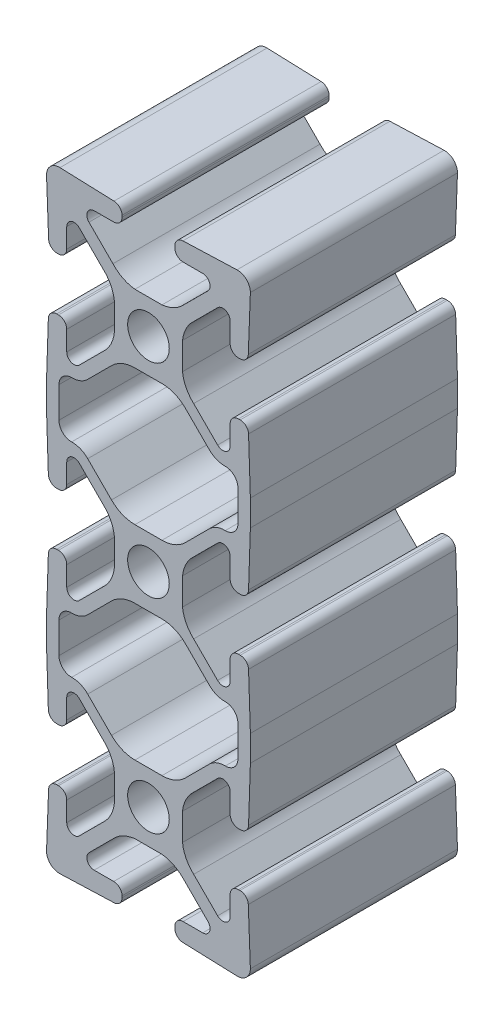
SolidWorks part; units mm, degrees
material "6061 Alloy"
ref_plane "Front" through (0, 0, 0) normal (0, 0, 1) x (1, 0, 0)
ref_plane "Top" through (0, 0, 0) normal (0, 1, 0) x (1, 0, 0)
ref_plane "Right" through (0, 0, 0) normal (1, 0, 0) x (0, 0, -1)
sketch "Sketch1" plane through (0, 0, 0) normal (0, 0, 1) x (1, 0, 0)
  line L0 (-7.4494, 41.7144) -> (-4.5322, 44.6317)
  line L1 (-1.6585, 45.822) -> (1.6585, 45.822)
  line L2 (-10.976, 35.6094) -> (-10.976, 39.3906)
  line L3 (4.5322, 44.6317) -> (7.4494, 41.7144)
  line L4 (-4.5322, 30.3683) -> (-7.4494, 33.2856)
  line L5 (10.976, 39.3906) -> (10.976, 35.6094)
  line L6 (1.6585, 29.178) -> (-1.6585, 29.178)
  line L7 (7.4494, 33.2856) -> (4.5322, 30.3683)
  line L8 (-12.5, 35.9125) -> (-12.5, 39.0875)
  line L9 (-12.2773, 29.22) -> (-12.5, 35.9125)
  line L10 (-12.5, 39.0875) -> (-12.2773, 45.78)
  line L11 (-11.036, 28.2385) -> (-11.2584, 28.2377)
  line L12 (-11.2584, 46.7622) -> (-11.036, 46.7615)
  line L13 (-10.02, 31.6575) -> (-10.02, 29.2545)
  line L14 (-10.02, 45.7455) -> (-10.02, 43.3425)
  line L15 (-5.5451, 29.3554) -> (-8.4836, 32.2939)
  line L16 (-8.4836, 42.7061) -> (-5.5451, 45.6446)
  line L17 (-4.178, 23.3415) -> (-4.178, 26.6585)
  line L18 (-4.178, 48.3415) -> (-4.178, 51.6585)
  line L19 (-8.4836, 17.7061) -> (-5.5451, 20.6446)
  line L20 (-5.5451, 54.3554) -> (-8.4836, 57.2939)
  line L21 (-10.02, 20.7455) -> (-10.02, 18.3425)
  line L22 (-10.02, 56.6575) -> (-10.02, 54.2545)
  line L23 (-11.2584, 21.7623) -> (-11.036, 21.7615)
  line L24 (-11.036, 53.2385) -> (-11.2263, 53.2379)
  line L25 (-12.5, 14.0875) -> (-12.2773, 20.78)
  line L26 (-12.2451, 54.2152) -> (-12.5, 60.9135)
  line L27 (-12.5, 10.9125) -> (-12.5, 14.0875)
  line L28 (-12.2773, 4.22) -> (-12.5, 10.9125)
  line L29 (-10.8555, 62.5) -> (-4.2218, 62.2615)
  line L30 (-11.036, 3.2385) -> (-11.2584, 3.2377)
  line L31 (-3.2385, 61.246) -> (-3.2385, 61.036)
  line L32 (-10.02, 6.6575) -> (-10.02, 4.2545)
  line L33 (-4.2545, 60.02) -> (-6.6575, 60.02)
  line L34 (-5.5451, 4.3554) -> (-8.4836, 7.2939)
  line L35 (-7.2939, 58.4836) -> (-4.3554, 55.5451)
  line L36 (-4.178, -1.6585) -> (-4.178, 1.6585)
  line L37 (-1.6585, 54.178) -> (1.6585, 54.178)
  line L38 (-8.4836, -7.2939) -> (-5.5451, -4.3554)
  line L39 (4.3554, 55.5451) -> (7.2939, 58.4836)
  line L40 (-10.02, -4.2545) -> (-10.02, -6.6575)
  line L41 (6.6575, 60.02) -> (4.2545, 60.02)
  line L42 (-11.2263, -3.2379) -> (-11.036, -3.2385)
  line L43 (3.2385, 61.036) -> (3.2385, 61.246)
  line L44 (-12.5, -10.9135) -> (-12.2451, -4.2152)
  line L45 (4.2218, 62.2615) -> (10.8555, 62.5)
  line L46 (-4.2218, -12.2615) -> (-10.8555, -12.5)
  line L47 (12.5, 60.9135) -> (12.2451, 54.2152)
  line L48 (-3.2385, -11.036) -> (-3.2385, -11.246)
  line L49 (11.2263, 53.2379) -> (11.036, 53.2385)
  line L50 (-6.6575, -10.02) -> (-4.2545, -10.02)
  line L51 (10.02, 54.2545) -> (10.02, 56.6575)
  line L52 (-4.3554, -5.5451) -> (-7.2939, -8.4836)
  line L53 (8.4836, 57.2939) -> (5.5451, 54.3554)
  line L54 (1.6585, -4.178) -> (-1.6585, -4.178)
  line L55 (4.178, 51.6585) -> (4.178, 48.3415)
  line L56 (7.2939, -8.4836) -> (4.3554, -5.5451)
  line L57 (5.5451, 45.6446) -> (8.4836, 42.7061)
  line L58 (4.2545, -10.02) -> (6.6575, -10.02)
  line L59 (10.02, 43.3425) -> (10.02, 45.7455)
  line L60 (3.2385, -11.246) -> (3.2385, -11.036)
  line L61 (11.036, 46.7615) -> (11.2584, 46.7622)
  line L62 (10.8555, -12.5) -> (4.2218, -12.2615)
  line L63 (12.2773, 45.78) -> (12.5, 39.0875)
  line L64 (12.5, 39.0875) -> (12.5, 35.9125)
  line L65 (12.2451, -4.2152) -> (12.5, -10.9135)
  line L66 (12.5, 35.9125) -> (12.2773, 29.22)
  line L67 (11.036, -3.2385) -> (11.2263, -3.2379)
  line L68 (11.2584, 28.2377) -> (11.036, 28.2385)
  line L69 (10.02, -6.6575) -> (10.02, -4.2545)
  line L70 (10.02, 29.2545) -> (10.02, 31.6575)
  line L71 (5.5451, -4.3554) -> (8.4836, -7.2939)
  line L72 (8.4836, 32.2939) -> (5.5451, 29.3554)
  line L73 (4.178, 1.6585) -> (4.178, -1.6585)
  line L74 (4.178, 26.6585) -> (4.178, 23.3415)
  line L75 (8.4836, 7.2939) -> (5.5451, 4.3554)
  line L76 (5.5451, 20.6446) -> (8.4836, 17.7061)
  line L77 (10.02, 4.2545) -> (10.02, 6.6575)
  line L78 (10.02, 18.3425) -> (10.02, 20.7455)
  line L79 (11.2584, 3.2377) -> (11.036, 3.2385)
  line L80 (11.036, 21.7615) -> (11.2584, 21.7623)
  line L81 (12.5, 10.9125) -> (12.2773, 4.22)
  line L82 (12.2773, 20.78) -> (12.5, 14.0875)
  line L83 (12.5, 14.0875) -> (12.5, 10.9125)
  line L84 (10.976, 14.3906) -> (10.976, 10.6094)
  line L85 (4.5322, 19.6317) -> (7.4494, 16.7144)
  line L86 (7.4494, 8.2856) -> (4.5322, 5.3683)
  line L87 (-1.6585, 20.822) -> (1.6585, 20.822)
  line L88 (1.6585, 4.178) -> (-1.6585, 4.178)
  line L89 (-7.4494, 16.7144) -> (-4.5322, 19.6317)
  line L90 (-4.5322, 5.3683) -> (-7.4494, 8.2856)
  line L91 (-10.976, 10.6094) -> (-10.976, 14.3906)
  arc A0 (-9.4184, 40.9142) -> (-7.4494, 41.7144) centre (-9.3594, 43.5917) ccw
  arc A1 (-1.6585, 45.822) -> (-4.5322, 44.6317) centre (-1.6585, 41.758) ccw
  arc A2 (-9.4184, 40.9142) -> (-10.976, 39.3906) centre (-9.452, 39.3906) ccw
  arc A3 (4.5322, 44.6317) -> (1.6585, 45.822) centre (1.6585, 41.758) ccw
  arc A4 (-10.976, 35.6094) -> (-9.4184, 34.0858) centre (-9.452, 35.6094) ccw
  arc A5 (-7.4494, 33.2856) -> (-9.4184, 34.0858) centre (-9.3594, 31.4083) ccw
  arc A6 (7.4494, 41.7144) -> (9.4184, 40.9142) centre (9.3594, 43.5917) ccw
  arc A7 (10.976, 39.3906) -> (9.4184, 40.9142) centre (9.452, 39.3906) ccw
  arc A8 (-4.5322, 30.3683) -> (-1.6585, 29.178) centre (-1.6585, 33.242) ccw
  arc A9 (9.4184, 34.0858) -> (10.976, 35.6094) centre (9.452, 35.6094) ccw
  arc A10 (1.6585, 29.178) -> (4.5322, 30.3683) centre (1.6585, 33.242) ccw
  arc A11 (9.4184, 34.0858) -> (7.4494, 33.2856) centre (9.3594, 31.4083) ccw
  arc A12 (-12.2773, 29.22) -> (-11.2584, 28.2377) centre (-11.2618, 29.2537) ccw
  arc A13 (-11.2584, 46.7622) -> (-12.2773, 45.78) centre (-11.2618, 45.7463) ccw
  arc A14 (-11.036, 28.2385) -> (-10.02, 29.2545) centre (-11.036, 29.2545) ccw
  arc A15 (-10.02, 45.7455) -> (-11.036, 46.7615) centre (-11.036, 45.7455) ccw
  arc A16 (-8.4836, 32.2939) -> (-10.02, 31.6575) centre (-9.12, 31.6575) ccw
  arc A17 (-10.02, 43.3425) -> (-8.4836, 42.7061) centre (-9.12, 43.3425) ccw
  arc A18 (-4.178, 26.6585) -> (-5.5451, 29.3554) centre (-8.422, 26.2021) ccw
  arc A19 (-5.5451, 45.6446) -> (-4.178, 48.3415) centre (-8.422, 48.7979) ccw
  arc A20 (-5.5451, 20.6446) -> (-4.178, 23.3415) centre (-8.422, 23.7979) ccw
  arc A21 (-4.178, 51.6585) -> (-5.5451, 54.3554) centre (-8.422, 51.2021) ccw
  arc A22 (-10.02, 18.3425) -> (-8.4836, 17.7061) centre (-9.12, 18.3425) ccw
  arc A23 (-8.4836, 57.2939) -> (-10.02, 56.6575) centre (-9.12, 56.6575) ccw
  arc A24 (-10.02, 20.7455) -> (-11.036, 21.7615) centre (-11.036, 20.7455) ccw
  arc A25 (-11.036, 53.2385) -> (-10.02, 54.2545) centre (-11.036, 54.2545) ccw
  arc A26 (-11.2584, 21.7623) -> (-12.2773, 20.78) centre (-11.2618, 20.7463) ccw
  arc A27 (-12.2451, 54.2152) -> (-11.2263, 53.2379) centre (-11.2298, 54.2539) ccw
  arc A28 (-10.8555, 62.5) -> (-12.5, 60.9135) centre (-10.9125, 60.9135) ccw
  arc A29 (-12.2773, 4.22) -> (-11.2584, 3.2377) centre (-11.2618, 4.2537) ccw
  arc A30 (-3.2385, 61.246) -> (-4.2218, 62.2615) centre (-4.2545, 61.246) ccw
  arc A31 (-11.036, 3.2385) -> (-10.02, 4.2545) centre (-11.036, 4.2545) ccw
  arc A32 (-4.2545, 60.02) -> (-3.2385, 61.036) centre (-4.2545, 61.036) ccw
  arc A33 (-8.4836, 7.2939) -> (-10.02, 6.6575) centre (-9.12, 6.6575) ccw
  arc A34 (-6.6575, 60.02) -> (-7.2939, 58.4836) centre (-6.6575, 59.12) ccw
  arc A35 (-4.178, 1.6585) -> (-5.5451, 4.3554) centre (-8.422, 1.2021) ccw
  arc A36 (-4.3554, 55.5451) -> (-1.6585, 54.178) centre (-1.2021, 58.422) ccw
  arc A37 (-5.5451, -4.3554) -> (-4.178, -1.6585) centre (-8.422, -1.2021) ccw
  arc A38 (1.6585, 54.178) -> (4.3554, 55.5451) centre (1.2021, 58.422) ccw
  arc A39 (-10.02, -6.6575) -> (-8.4836, -7.2939) centre (-9.12, -6.6575) ccw
  arc A40 (7.2939, 58.4836) -> (6.6575, 60.02) centre (6.6575, 59.12) ccw
  arc A41 (-10.02, -4.2545) -> (-11.036, -3.2385) centre (-11.036, -4.2545) ccw
  arc A42 (3.2385, 61.036) -> (4.2545, 60.02) centre (4.2545, 61.036) ccw
  arc A43 (-11.2263, -3.2379) -> (-12.2451, -4.2152) centre (-11.2298, -4.2539) ccw
  arc A44 (4.2218, 62.2615) -> (3.2385, 61.246) centre (4.2545, 61.246) ccw
  arc A45 (-12.5, -10.9135) -> (-10.8555, -12.5) centre (-10.9125, -10.9135) ccw
  arc A46 (12.5, 60.9135) -> (10.8555, 62.5) centre (10.9125, 60.9135) ccw
  arc A47 (-4.2218, -12.2615) -> (-3.2385, -11.246) centre (-4.2545, -11.246) ccw
  arc A48 (11.2263, 53.2379) -> (12.2451, 54.2152) centre (11.2298, 54.2539) ccw
  arc A49 (-3.2385, -11.036) -> (-4.2545, -10.02) centre (-4.2545, -11.036) ccw
  arc A50 (10.02, 54.2545) -> (11.036, 53.2385) centre (11.036, 54.2545) ccw
  arc A51 (-7.2939, -8.4836) -> (-6.6575, -10.02) centre (-6.6575, -9.12) ccw
  arc A52 (10.02, 56.6575) -> (8.4836, 57.2939) centre (9.12, 56.6575) ccw
  arc A53 (-1.6585, -4.178) -> (-4.3554, -5.5451) centre (-1.2021, -8.422) ccw
  arc A54 (5.5451, 54.3554) -> (4.178, 51.6585) centre (8.422, 51.2021) ccw
  arc A55 (4.3554, -5.5451) -> (1.6585, -4.178) centre (1.2021, -8.422) ccw
  arc A56 (4.178, 48.3415) -> (5.5451, 45.6446) centre (8.422, 48.7979) ccw
  arc A57 (6.6575, -10.02) -> (7.2939, -8.4836) centre (6.6575, -9.12) ccw
  arc A58 (8.4836, 42.7061) -> (10.02, 43.3425) centre (9.12, 43.3425) ccw
  arc A59 (4.2545, -10.02) -> (3.2385, -11.036) centre (4.2545, -11.036) ccw
  arc A60 (11.036, 46.7615) -> (10.02, 45.7455) centre (11.036, 45.7455) ccw
  arc A61 (3.2385, -11.246) -> (4.2218, -12.2615) centre (4.2545, -11.246) ccw
  arc A62 (12.2773, 45.78) -> (11.2584, 46.7622) centre (11.2618, 45.7463) ccw
  arc A63 (10.8555, -12.5) -> (12.5, -10.9135) centre (10.9125, -10.9135) ccw
  arc A64 (12.2451, -4.2152) -> (11.2263, -3.2379) centre (11.2298, -4.2539) ccw
  arc A65 (11.2584, 28.2377) -> (12.2773, 29.22) centre (11.2618, 29.2537) ccw
  arc A66 (11.036, -3.2385) -> (10.02, -4.2545) centre (11.036, -4.2545) ccw
  arc A67 (10.02, 29.2545) -> (11.036, 28.2385) centre (11.036, 29.2545) ccw
  arc A68 (8.4836, -7.2939) -> (10.02, -6.6575) centre (9.12, -6.6575) ccw
  arc A69 (10.02, 31.6575) -> (8.4836, 32.2939) centre (9.12, 31.6575) ccw
  arc A70 (4.178, -1.6585) -> (5.5451, -4.3554) centre (8.422, -1.2021) ccw
  arc A71 (5.5451, 29.3554) -> (4.178, 26.6585) centre (8.422, 26.2021) ccw
  arc A72 (5.5451, 4.3554) -> (4.178, 1.6585) centre (8.422, 1.2021) ccw
  arc A73 (4.178, 23.3415) -> (5.5451, 20.6446) centre (8.422, 23.7979) ccw
  arc A74 (10.02, 6.6575) -> (8.4836, 7.2939) centre (9.12, 6.6575) ccw
  arc A75 (8.4836, 17.7061) -> (10.02, 18.3425) centre (9.12, 18.3425) ccw
  arc A76 (10.02, 4.2545) -> (11.036, 3.2385) centre (11.036, 4.2545) ccw
  arc A77 (11.036, 21.7615) -> (10.02, 20.7455) centre (11.036, 20.7455) ccw
  arc A78 (11.2584, 3.2377) -> (12.2773, 4.22) centre (11.2618, 4.2537) ccw
  arc A79 (12.2773, 20.78) -> (11.2584, 21.7623) centre (11.2618, 20.7463) ccw
  arc A80 (10.976, 14.3906) -> (9.4184, 15.9142) centre (9.452, 14.3906) ccw
  arc A81 (9.4184, 9.0858) -> (10.976, 10.6094) centre (9.452, 10.6094) ccw
  arc A82 (7.4494, 16.7144) -> (9.4184, 15.9142) centre (9.3594, 18.5917) ccw
  arc A83 (9.4184, 9.0858) -> (7.4494, 8.2856) centre (9.3594, 6.4083) ccw
  arc A84 (4.5322, 19.6317) -> (1.6585, 20.822) centre (1.6585, 16.758) ccw
  arc A85 (1.6585, 4.178) -> (4.5322, 5.3683) centre (1.6585, 8.242) ccw
  arc A86 (-1.6585, 20.822) -> (-4.5322, 19.6317) centre (-1.6585, 16.758) ccw
  arc A87 (-4.5322, 5.3683) -> (-1.6585, 4.178) centre (-1.6585, 8.242) ccw
  arc A88 (-9.4184, 15.9142) -> (-7.4494, 16.7144) centre (-9.3594, 18.5917) ccw
  arc A89 (-7.4494, 8.2856) -> (-9.4184, 9.0858) centre (-9.3594, 6.4083) ccw
  arc A90 (-9.4184, 15.9142) -> (-10.976, 14.3906) centre (-9.452, 14.3906) ccw
  arc A91 (-10.976, 10.6094) -> (-9.4184, 9.0858) centre (-9.452, 10.6094) ccw
  circle A92 centre (0, 0) radius 2.5527
  circle A93 centre (0, 25) radius 2.5527
  circle A94 centre (0, 50) radius 2.5527
extrude "Extrude1" add sketch "Sketch1" along normal blind 25.4
